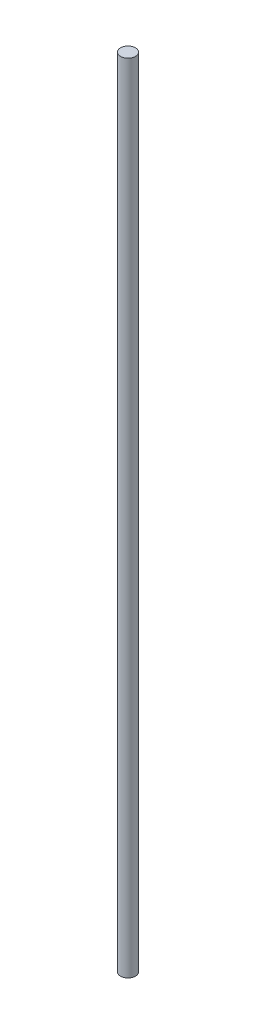
SolidWorks part; units mm, degrees
ref_plane "Front Plane" through (0, 0, 0) normal (0, 0, 1) x (1, 0, 0)
ref_plane "Top Plane" through (0, 0, 0) normal (0, 1, 0) x (1, 0, 0)
ref_plane "Right Plane" through (0, 0, 0) normal (1, 0, 0) x (0, 0, -1)
sketch "Sketch1" plane through (0, 0, 0) normal (0, 1, 0) x (1, 0, 0)
  circle A0 centre (0, 0) radius 2.3813
  dimension "D1" = 4.7625
extrude "Boss-Extrude1" add sketch "Sketch1" along normal blind 254
